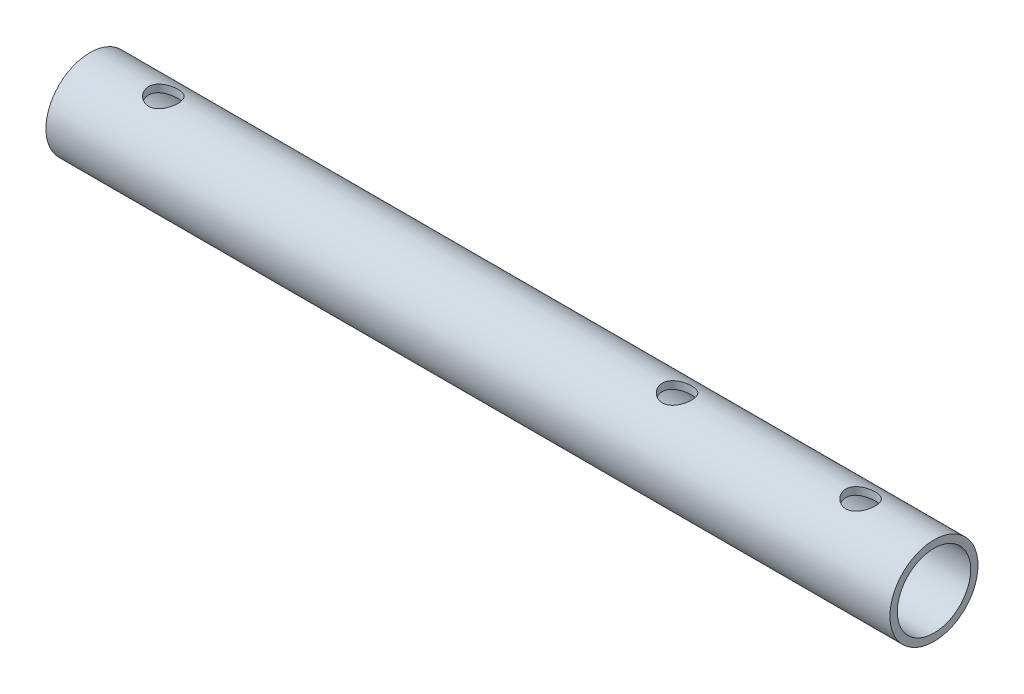
SolidWorks part; units mm, degrees
ref_plane "Front Plane" through (0, 0, 0) normal (0, 0, 1) x (1, 0, 0)
ref_plane "Top Plane" through (0, 0, 0) normal (0, 1, 0) x (1, 0, 0)
ref_plane "Right Plane" through (0, 0, 0) normal (1, 0, 0) x (0, 0, -1)
sketch "Sketch1" plane through (0, 0, 0) normal (1, 0, 0) x (0, 0, -1)
  circle A0 centre (0, 0) radius 6
  circle A1 centre (0, 0) radius 5
  dimension "D1" = 12
  dimension "D2" = 10
extrude "Boss-Extrude1" add sketch "Sketch1" along normal mid plane 90
sketch "Sketch3" plane through (45, 0, 0) normal (1, 0, 0) x (0, 0, -1)
  circle A0 centre (0, 0) radius 6
  circle A1 centre (0, 0) radius 5
extrude "Boss-Extrude2" add sketch "Sketch3" along normal blind 25
sketch "Sketch2" plane through (0, 0, 0) normal (0, 1, 0) x (1, 0, 0)
  line L0 (-45, 0) -> (-35, 0) construction
  line L1 (-45, 6) -> (-45, -6) construction
  line L2 (0, -6.6) -> (0, 6.6) construction
  line L3 (70, 0) -> (60, 0) construction
  line L5 (70, -6) -> (70, 6) construction
  circle A0 centre (-35, 0) radius 2
  circle A1 centre (35, 0) radius 2
  circle A3 centre (60, 0) radius 2
  dimension "D2" = 4
  dimension "D4" = 4
  dimension "D1" = 10
  dimension "D3" = 10
extrude "Cut-Extrude1" cut sketch "Sketch2" against normal mid plane 20
